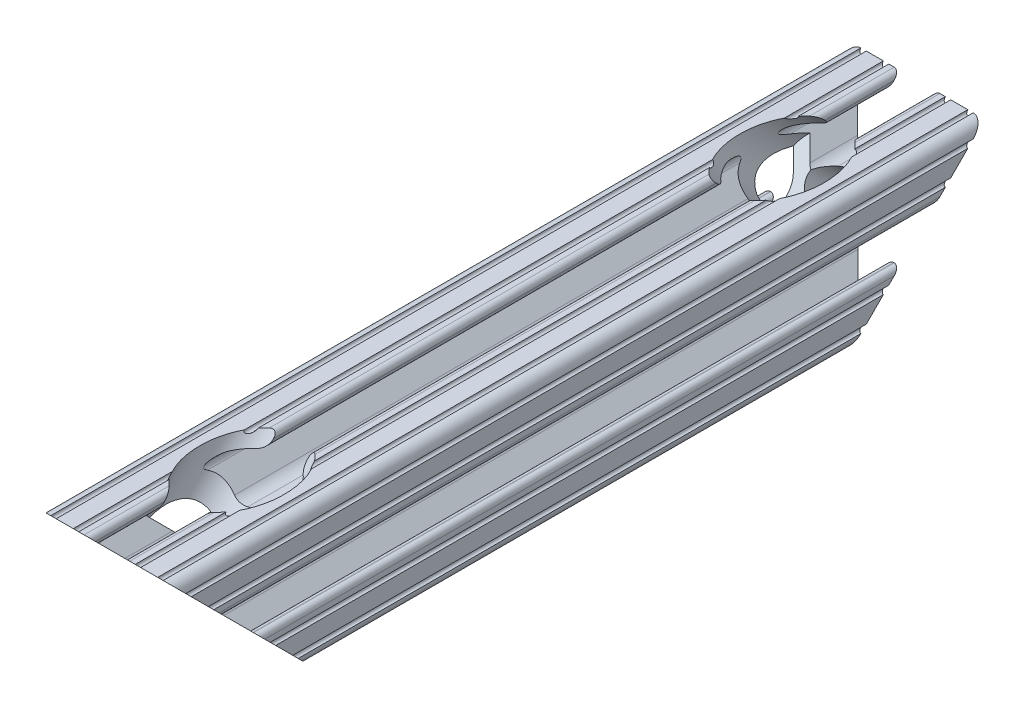
SolidWorks part; units mm, degrees
ref_plane "Front Plane" through (0, 0, 0) normal (0, 0, 1) x (1, 0, 0)
ref_plane "Top Plane" through (0, 0, 0) normal (0, 1, 0) x (1, 0, 0)
ref_plane "Right Plane" through (0, 0, 0) normal (1, 0, 0) x (0, 0, -1)
sketch "Sketch1" plane through (0, 0, 0) normal (0, 0, 1) x (1, 0, 0)
  line L2 (-7.1797, -8.6452) -> (-3.9523, -5.4237)
  line L3 (-1.7093, -4.4958) -> (1.7093, -4.4958)
  line L4 (3.9523, -5.4237) -> (7.1797, -8.6452)
  line L6 (6.4164, -10.4902) -> (4.2875, -10.4902)
  line L7 (3.2385, -11.5392) -> (3.2385, -11.651)
  line L8 (4.2875, -12.7) -> (5.3171, -12.7)
  line L9 (6.3331, -12.7) -> (9.5504, -12.7)
  line L10 (12.7, -9.5504) -> (12.7, -6.3331)
  line L11 (12.7, -5.3171) -> (12.7, -4.2875)
  line L12 (11.651, -3.2385) -> (11.5392, -3.2385)
  line L13 (10.4902, -4.2875) -> (10.4902, -6.4021)
  line L14 (8.7371, -7.1294) -> (5.441, -3.8408)
  line L15 (4.5085, -1.5932) -> (4.5085, 1.5932)
  line L16 (5.441, 3.8408) -> (8.7371, 7.1294)
  line L17 (10.4902, 6.4021) -> (10.4902, 4.2875)
  line L18 (11.5392, 3.2385) -> (11.651, 3.2385)
  line L19 (12.7, 4.2875) -> (12.7, 5.3171)
  line L20 (12.7, 6.3331) -> (12.7, 9.5504)
  line L21 (9.5504, 12.7) -> (6.3331, 12.7)
  line L22 (5.3171, 12.7) -> (4.2875, 12.7)
  line L23 (3.2385, 11.651) -> (3.2385, 11.5392)
  line L24 (4.2875, 10.4902) -> (6.4768, 10.4902)
  line L25 (7.207, 8.7244) -> (3.8983, 5.4232)
  line L26 (1.6558, 4.4958) -> (-1.6558, 4.4958)
  line L27 (-3.8983, 5.4232) -> (-7.207, 8.7244)
  line L28 (-6.4768, 10.4902) -> (-4.2875, 10.4902)
  line L29 (-3.2385, 11.5392) -> (-3.2385, 11.651)
  line L30 (-4.2875, 12.7) -> (-5.3171, 12.7)
  line L31 (-6.3331, 12.7) -> (-9.5504, 12.7)
  line L32 (-12.7, 9.5504) -> (-12.7, 6.3331)
  line L33 (-12.7, 5.3171) -> (-12.7, 4.2875)
  line L34 (-11.651, 3.2385) -> (-11.5392, 3.2385)
  line L35 (-10.4902, 4.2875) -> (-10.4902, 6.4021)
  line L36 (-8.7371, 7.1294) -> (-5.441, 3.8408)
  line L37 (-4.5085, 1.5932) -> (-4.5085, -1.5932)
  line L38 (-5.441, -3.8408) -> (-8.7371, -7.1294)
  line L39 (-10.4902, -6.4021) -> (-10.4902, -4.2875)
  line L40 (-11.5392, -3.2385) -> (-11.651, -3.2385)
  line L41 (-12.7, -4.2875) -> (-12.7, -5.3171)
  line L42 (-12.7, -6.3331) -> (-12.7, -9.5504)
  line L43 (-9.5504, -12.7) -> (-6.3331, -12.7)
  line L44 (-5.3171, -12.7) -> (-4.2875, -12.7)
  line L45 (-3.2385, -11.651) -> (-3.2385, -11.5392)
  line L46 (-4.2875, -10.4902) -> (-6.4164, -10.4902)
  circle A0 centre (0, 0) radius 2.6035
  arc A1 (-7.1797, -8.6452) -> (-6.4164, -10.4902) centre (-6.4164, -9.4098) ccw
  arc A2 (-1.7093, -4.4958) -> (-3.9523, -5.4237) centre (-1.7093, -7.6708) ccw
  arc A3 (3.9523, -5.4237) -> (1.7093, -4.4958) centre (1.7093, -7.6708) ccw
  arc A4 (6.4164, -10.4902) -> (7.1797, -8.6452) centre (6.4164, -9.4098) ccw
  arc A5 (4.2875, -10.4902) -> (3.2385, -11.5392) centre (4.2875, -11.5392) ccw
  arc A6 (3.2385, -11.651) -> (4.2875, -12.7) centre (4.2875, -11.651) ccw
  arc A7 (6.3331, -12.7) -> (5.3171, -12.7) centre (5.8251, -12.7) ccw
  arc A8 (10.5664, -12.6998) -> (9.5504, -12.7) centre (10.0584, -12.7) ccw
  arc A9 (10.5664, -12.6998) -> (12.6998, -10.5664) centre (10.5918, -10.5918) ccw
  arc A10 (12.7, -9.5504) -> (12.6998, -10.5664) centre (12.7, -10.0584) ccw
  arc A11 (12.7, -5.3171) -> (12.7, -6.3331) centre (12.7, -5.8251) ccw
  arc A12 (12.7, -4.2875) -> (11.651, -3.2385) centre (11.651, -4.2875) ccw
  arc A13 (11.5392, -3.2385) -> (10.4902, -4.2875) centre (11.5392, -4.2875) ccw
  arc A14 (8.7371, -7.1294) -> (10.4902, -6.4021) centre (9.4628, -6.4021) ccw
  arc A15 (4.5085, -1.5932) -> (5.441, -3.8408) centre (7.6835, -1.5932) ccw
  arc A16 (5.441, 3.8408) -> (4.5085, 1.5932) centre (7.6835, 1.5932) ccw
  arc A17 (10.4902, 6.4021) -> (8.7371, 7.1294) centre (9.4628, 6.4021) ccw
  arc A18 (10.4902, 4.2875) -> (11.5392, 3.2385) centre (11.5392, 4.2875) ccw
  arc A19 (11.651, 3.2385) -> (12.7, 4.2875) centre (11.651, 4.2875) ccw
  arc A20 (12.7, 6.3331) -> (12.7, 5.3171) centre (12.7, 5.8251) ccw
  arc A21 (12.6998, 10.5664) -> (12.7, 9.5504) centre (12.7, 10.0584) ccw
  arc A22 (12.6998, 10.5664) -> (10.5664, 12.6998) centre (10.5918, 10.5918) ccw
  arc A23 (9.5504, 12.7) -> (10.5664, 12.6998) centre (10.0584, 12.7) ccw
  arc A24 (5.3171, 12.7) -> (6.3331, 12.7) centre (5.8251, 12.7) ccw
  arc A25 (4.2875, 12.7) -> (3.2385, 11.651) centre (4.2875, 11.651) ccw
  arc A26 (3.2385, 11.5392) -> (4.2875, 10.4902) centre (4.2875, 11.5392) ccw
  arc A27 (7.207, 8.7244) -> (6.4768, 10.4902) centre (6.4768, 9.4563) ccw
  arc A28 (1.6558, 4.4958) -> (3.8983, 5.4232) centre (1.6558, 7.6708) ccw
  arc A29 (-3.8983, 5.4232) -> (-1.6558, 4.4958) centre (-1.6558, 7.6708) ccw
  arc A30 (-6.4768, 10.4902) -> (-7.207, 8.7244) centre (-6.4768, 9.4563) ccw
  arc A31 (-4.2875, 10.4902) -> (-3.2385, 11.5392) centre (-4.2875, 11.5392) ccw
  arc A32 (-3.2385, 11.651) -> (-4.2875, 12.7) centre (-4.2875, 11.651) ccw
  arc A33 (-6.3331, 12.7) -> (-5.3171, 12.7) centre (-5.8251, 12.7) ccw
  arc A34 (-10.5664, 12.6998) -> (-9.5504, 12.7) centre (-10.0584, 12.7) ccw
  arc A35 (-10.5664, 12.6998) -> (-12.6998, 10.5664) centre (-10.5918, 10.5918) ccw
  arc A36 (-12.7, 9.5504) -> (-12.6998, 10.5664) centre (-12.7, 10.0584) ccw
  arc A37 (-12.7, 5.3171) -> (-12.7, 6.3331) centre (-12.7, 5.8251) ccw
  arc A38 (-12.7, 4.2875) -> (-11.651, 3.2385) centre (-11.651, 4.2875) ccw
  arc A39 (-11.5392, 3.2385) -> (-10.4902, 4.2875) centre (-11.5392, 4.2875) ccw
  arc A40 (-8.7371, 7.1294) -> (-10.4902, 6.4021) centre (-9.4628, 6.4021) ccw
  arc A41 (-4.5085, 1.5932) -> (-5.441, 3.8408) centre (-7.6835, 1.5932) ccw
  arc A42 (-5.441, -3.8408) -> (-4.5085, -1.5932) centre (-7.6835, -1.5932) ccw
  arc A43 (-10.4902, -6.4021) -> (-8.7371, -7.1294) centre (-9.4628, -6.4021) ccw
  arc A44 (-10.4902, -4.2875) -> (-11.5392, -3.2385) centre (-11.5392, -4.2875) ccw
  arc A45 (-11.651, -3.2385) -> (-12.7, -4.2875) centre (-11.651, -4.2875) ccw
  arc A46 (-12.7, -6.3331) -> (-12.7, -5.3171) centre (-12.7, -5.8251) ccw
  arc A47 (-12.6998, -10.5664) -> (-12.7, -9.5504) centre (-12.7, -10.0584) ccw
  arc A48 (-12.6998, -10.5664) -> (-10.5664, -12.6998) centre (-10.5918, -10.5918) ccw
  arc A49 (-9.5504, -12.7) -> (-10.5664, -12.6998) centre (-10.0584, -12.7) ccw
  arc A50 (-5.3171, -12.7) -> (-6.3331, -12.7) centre (-5.8251, -12.7) ccw
  arc A51 (-4.2875, -12.7) -> (-3.2385, -11.651) centre (-4.2875, -11.651) ccw
  arc A52 (-3.2385, -11.5392) -> (-4.2875, -10.4902) centre (-4.2875, -11.5392) ccw
extrude "Boss-Extrude1" add sketch "Sketch1" along normal mid plane 152.4
sketch "Sketch2" plane through (0, 0, 0) normal (1, 0, 0) x (0, 0, -1)
  line L0 (-76.2, 12.6998) -> (-76.2, -12.7)
  line L1 (-76.2, -12.7) -> (-50.8002, -12.7)
  line L2 (-50.8002, -12.7) -> (-76.2, 12.6998)
  line L3 (0, 0) -> (0, -12.7) construction
  line L5 (50.8002, -12.7) -> (76.2, 12.6998)
  line L6 (76.2, -12.7) -> (50.8002, -12.7)
  line L7 (76.2, 12.6998) -> (76.2, -12.7)
  line L8 (-76.2, -12.7) -> (76.2, -12.7) construction
extrude "Cut-Extrude1" cut sketch "Sketch2" against normal through all and the other way through all
sketch "Sketch3" plane through (0, 0, 0) normal (1, 0, 0) x (0, 0, -1)
  line L0 (-45.1876, 18.3125) -> (-63.5002, 0)
  line L1 (-63.5002, 0) -> (-65.8081, 2.3079)
  line L2 (-65.8081, 2.3079) -> (-61.318, 6.7981)
  line L3 (-61.318, 6.7981) -> (-64.6227, 10.1028)
  line L4 (-64.6227, 10.1028) -> (-50.8003, 23.9252)
  line L5 (-50.8003, 23.9252) -> (-45.1876, 18.3125)
  line L6 (-63.5002, 0) -> (-65.8081, -2.3079) construction
  line L7 (-50.8002, -12.7) -> (-76.2, 12.6998) construction
  line L8 (-66.1037, 2.6035) -> (-60.8967, -2.6035) construction
  line L9 (-53.3974, -1.1225) -> (-39.575, 12.6998) construction
  dimension "D1" = 6.5278
  dimension "D2" = 15.875
  dimension "D3" = 6.35
revolve "Cut-Revolve1" cut sketch "Sketch3" angle 360 mid plane about L6
mirror "Mirror1" about plane through (0, 0, 0) normal (0, 0, 1) of "Cut-Revolve1"
